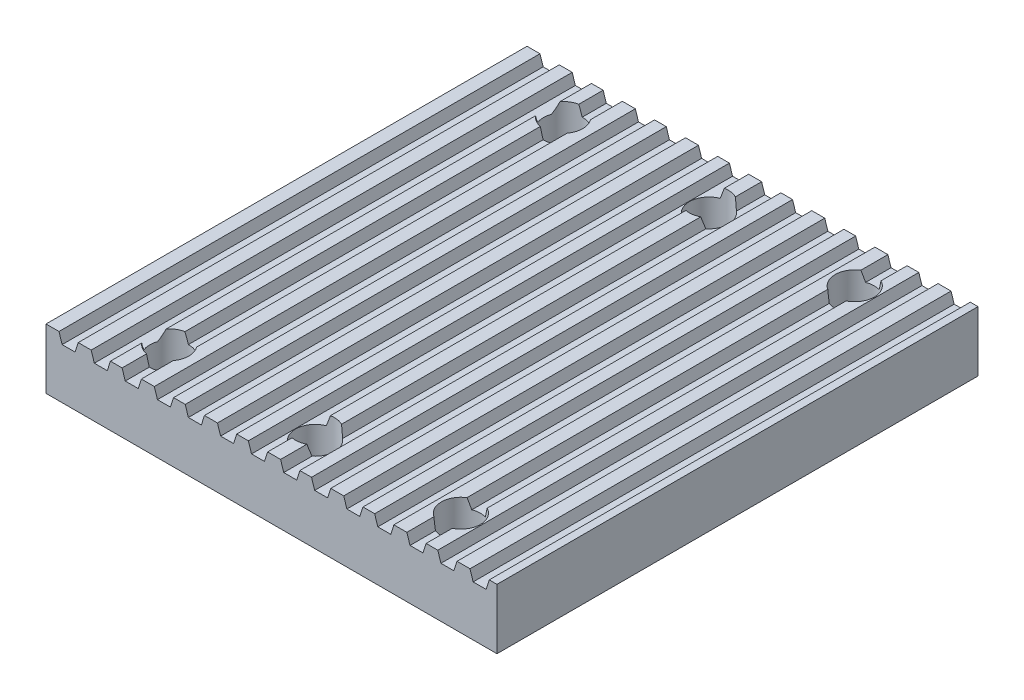
SolidWorks part; units mm, degrees
ref_plane "Front Plane" through (0, 0, 0) normal (0, 0, 1) x (1, 0, 0)
ref_plane "Top Plane" through (0, 0, 0) normal (0, 1, 0) x (1, 0, 0)
ref_plane "Right Plane" through (0, 0, 0) normal (1, 0, 0) x (0, 0, -1)
sketch "Sketch1" plane through (0, 0, 0) normal (0, 1, 0) x (1, 0, 0)
  line L0 (-798.1092, 0) -> (701.8908, 0)
  line L1 (701.8908, 0) -> (701.8908, 1600)
  line L2 (701.8908, 1600) -> (-798.1092, 1600)
  line L3 (-798.1092, 1600) -> (-798.1092, 0)
  line L4 (-798.1092, 800) -> (701.8908, 800) construction
  circle A0 centre (436.8908, 1455) radius 65
  circle A1 centre (-48.1092, 1455) radius 65
  circle A2 centre (-533.1092, 1455) radius 65
  circle A3 centre (436.8908, 145) radius 65
  circle A4 centre (-48.1092, 145) radius 65
  circle A5 centre (-533.1092, 145) radius 65
  dimension "D6" = 130
  dimension "D1" = 1600
  dimension "D2" = 1500
  dimension "D3" = 265
  dimension "D4" = 265
  dimension "D5" = 485
  dimension "D7" = 145
extrude "Boss-Extrude1" add sketch "Sketch1" along normal blind 200
sketch "Sketch3" plane through (0, 0, 0) normal (0, 0, 1) x (1, 0, 0)
  line L0 (-798.1092, 200) -> (-754.9569, 200)
  line L1 (-798.1092, 200) -> (701.8908, 200) construction
  line L2 (-754.9569, 200) -> (-744.5378, 167.3588)
  line L3 (-744.5378, 167.3588) -> (-701.3854, 167.3588)
  line L4 (-701.3854, 167.3588) -> (-690.9664, 200)
  line L5 (-690.9664, 200) -> (-647.814, 200)
  line L6 (-647.814, 200) -> (-637.395, 167.3588)
  line L7 (-637.395, 167.3588) -> (-594.2426, 167.3588)
  line L8 (-594.2426, 167.3588) -> (-583.8235, 200)
  line L9 (-588.1092, 200) -> (-544.9569, 200)
  line L10 (-544.9569, 200) -> (-534.5378, 167.3588)
  line L11 (-491.3854, 167.3588) -> (-480.9664, 200)
  line L12 (-534.5378, 167.3588) -> (-491.3854, 167.3588)
  line L13 (-480.9664, 200) -> (-437.814, 200)
  line L14 (-437.814, 200) -> (-427.395, 167.3588)
  line L15 (-427.395, 167.3588) -> (-384.2426, 167.3588)
  line L16 (-384.2426, 167.3588) -> (-373.8235, 200)
  line L17 (-378.1092, 200) -> (-334.9569, 200)
  line L18 (-334.9569, 200) -> (-324.5378, 167.3588)
  line L19 (-281.3854, 167.3588) -> (-270.9664, 200)
  line L20 (-324.5378, 167.3588) -> (-281.3854, 167.3588)
  line L21 (-270.9664, 200) -> (-227.814, 200)
  line L22 (-227.814, 200) -> (-217.395, 167.3588)
  line L23 (-217.395, 167.3588) -> (-174.2426, 167.3588)
  line L24 (-174.2426, 167.3588) -> (-163.8235, 200)
  line L25 (-168.1092, 200) -> (-124.9569, 200)
  line L26 (-124.9569, 200) -> (-114.5378, 167.3588)
  line L27 (-71.3854, 167.3588) -> (-60.9664, 200)
  line L28 (-114.5378, 167.3588) -> (-71.3854, 167.3588)
  line L29 (-60.9664, 200) -> (-17.814, 200)
  line L30 (-17.814, 200) -> (-7.395, 167.3588)
  line L31 (-7.395, 167.3588) -> (35.7574, 167.3588)
  line L32 (35.7574, 167.3588) -> (46.1765, 200)
  line L33 (41.8908, 200) -> (85.0431, 200)
  line L34 (85.0431, 200) -> (95.4622, 167.3588)
  line L35 (138.6146, 167.3588) -> (149.0336, 200)
  line L36 (95.4622, 167.3588) -> (138.6146, 167.3588)
  line L37 (149.0336, 200) -> (192.186, 200)
  line L38 (192.186, 200) -> (202.605, 167.3588)
  line L39 (202.605, 167.3588) -> (245.7574, 167.3588)
  line L40 (245.7574, 167.3588) -> (256.1765, 200)
  line L41 (251.8908, 200) -> (295.0431, 200)
  line L42 (295.0431, 200) -> (305.4622, 167.3588)
  line L43 (348.6146, 167.3588) -> (359.0336, 200)
  line L44 (305.4622, 167.3588) -> (348.6146, 167.3588)
  line L45 (359.0336, 200) -> (402.186, 200)
  line L46 (402.186, 200) -> (412.605, 167.3588)
  line L47 (412.605, 167.3588) -> (455.7574, 167.3588)
  line L48 (455.7574, 167.3588) -> (466.1765, 200)
  line L49 (461.8908, 200) -> (505.0431, 200)
  line L50 (505.0431, 200) -> (515.4622, 167.3588)
  line L51 (558.6146, 167.3588) -> (569.0336, 200)
  line L52 (515.4622, 167.3588) -> (558.6146, 167.3588)
  line L53 (569.0336, 200) -> (612.186, 200)
  line L54 (612.186, 200) -> (622.605, 167.3588)
  line L55 (622.605, 167.3588) -> (665.7574, 167.3588)
  line L56 (665.7574, 167.3588) -> (676.1765, 200)
  line L57 (-798.1092, 200) -> (-588.1092, 200) construction
  line L58 (-754.9569, 200) -> (701.8908, 200)
  dimension "D1" = 214.2857
  dimension "D2" = 210
  dimension "D3" = 7
extrude "Cut-Extrude1" cut sketch "Sketch3" against normal through all and the other way through all contours L3 L4 L12 L2 | L7 L8 L12 L6 | L10 L12 L11 | L15 L16 L12 L14 | L18 L20 L19 L12 | L23 L24 L12 L22 | L26 L28 L27 L12 | L31 L32 L12 L30 | L34 L36 L35 L12 | L39 L40 L12 L38 | L42 L44 L43 L12 | L47 L48 L12 L46 | L50 L52 L51 L12 | L55 L56 L12 L54
sketch "Sketch4" plane through (0, 0, 0) normal (0, 0, 1) x (1, 0, 0)
